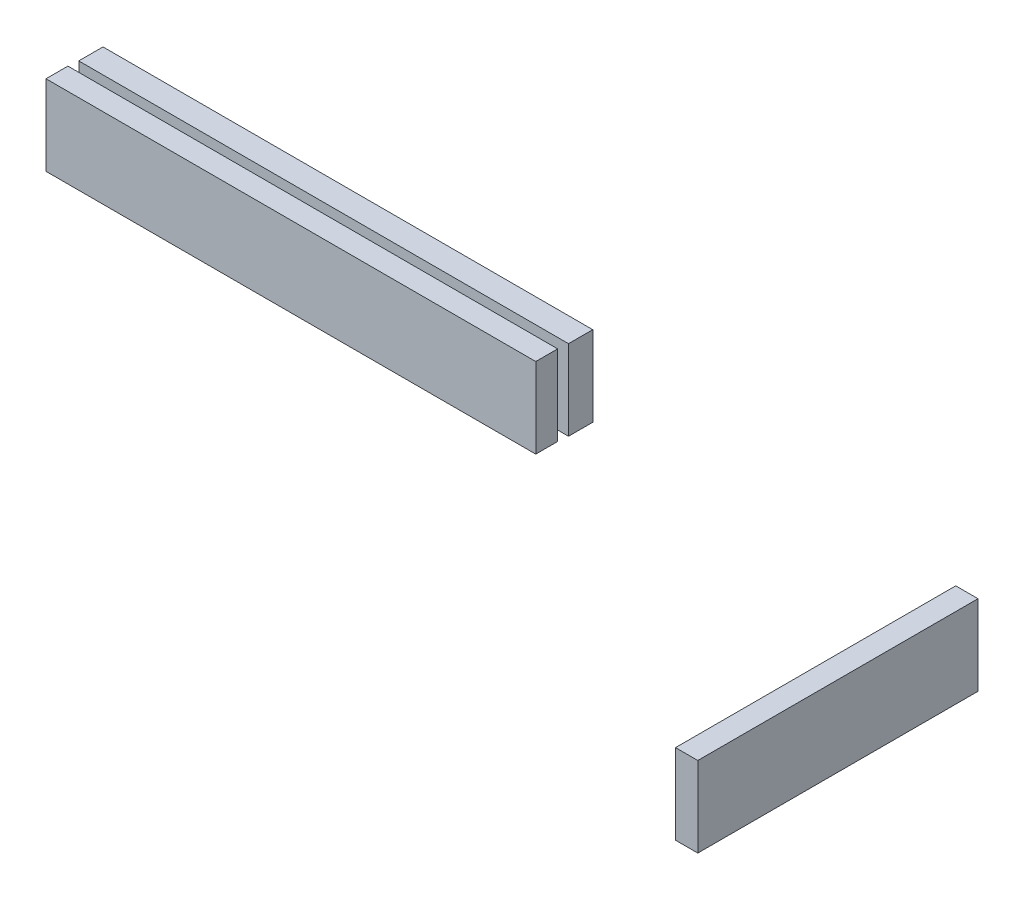
SolidWorks part; units mm, degrees
ref_plane "Front Plane" through (0, 0, 0) normal (0, 0, 1) x (1, 0, 0)
ref_plane "Top Plane" through (0, 0, 0) normal (0, 1, 0) x (1, 0, 0)
ref_plane "Right Plane" through (0, 0, 0) normal (1, 0, 0) x (0, 0, -1)
sketch "Sketch1" plane through (0, 0, 0) normal (0, 1, 0) x (1, 0, 0)
  line L0 (-37.8462, 13.1574) -> (23.2072, 13.1574)
  line L1 (-37.9599, 9.188) -> (23.0935, 9.188)
  line L2 (-37.9599, 9.188) -> (-37.9599, 11.9197)
  line L3 (-37.9599, 11.9197) -> (23.0935, 11.9197)
  line L4 (23.0935, 9.188) -> (23.0935, 11.9197)
  line L5 (-37.9599, 9.188) -> (23.0935, 11.9197) construction
  line L6 (-37.9599, 11.9197) -> (23.0935, 9.188) construction
  line L7 (-37.8462, 13.1574) -> (-37.8462, 16.1799)
  line L8 (-37.8462, 16.1799) -> (23.2072, 16.1799)
  line L9 (23.2072, 13.1574) -> (23.2072, 16.1799)
  line L10 (76.2645, -23.7827) -> (76.2645, 11.1477)
  line L11 (76.2645, -23.7827) -> (73.4876, -23.7827)
  line L12 (73.4876, -23.7827) -> (73.4876, 11.1477)
  line L13 (76.2645, 11.1477) -> (73.4876, 11.1477)
  point P0 (-7.4332, 10.5538)
extrude "Boss-Extrude1" add sketch "Sketch1" along normal blind 10
